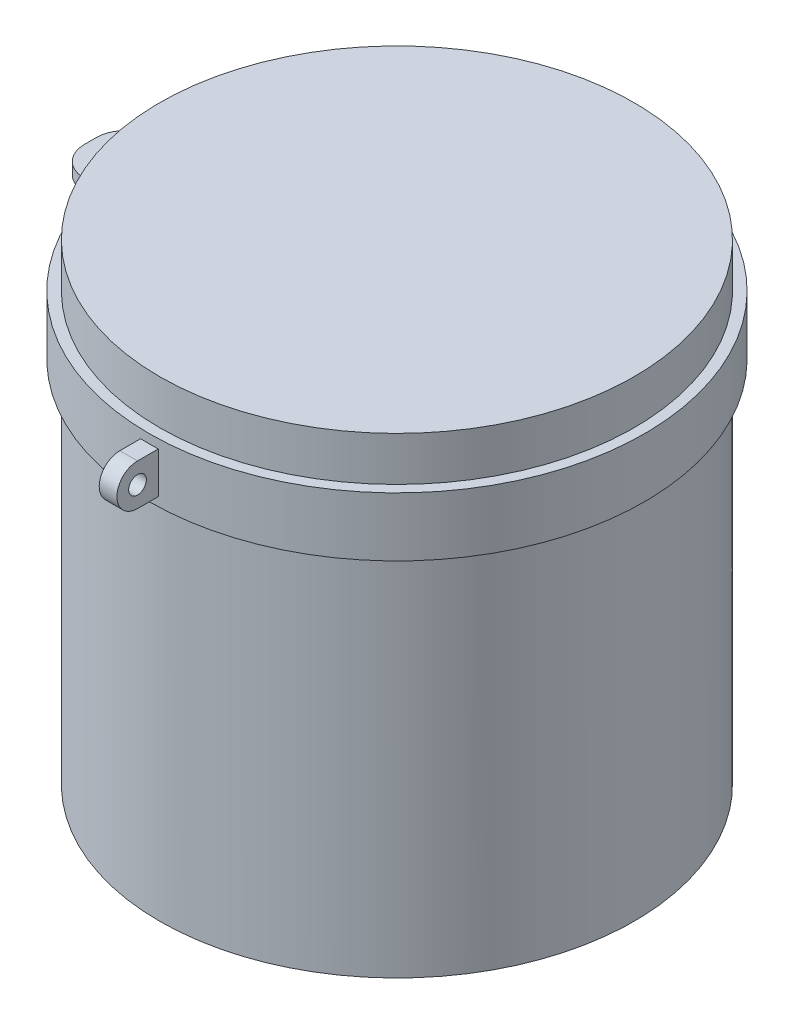
SolidWorks part; units mm, degrees
material "Серое литое железо (SN)"
ref_plane "Спереди" through (0, 0, 0) normal (0, 0, 1) x (1, 0, 0)
ref_plane "Сверху" through (0, 0, 0) normal (0, 1, 0) x (1, 0, 0)
ref_plane "Справа" through (0, 0, 0) normal (1, 0, 0) x (0, 0, -1)
sketch "Эскиз2" plane through (0, 0, 0) normal (0, 0, 1) x (1, 0, 0)
  line L0 (0, 1662.873) -> (0, -74.6932) construction
  line L2 (-800, 1450) -> (-840, 1450)
  line L3 (-800, 1450) -> (-800, 1250)
  line L4 (-800, 1250) -> (-840, 1250)
  line L5 (-840, 1450) -> (-840, 1250)
  line L6 (-975.1647, 0) -> (926.4065, 0) construction
  point P11 (0, 0)
  dimension "D1" = 800
  dimension "D2" = 200
  dimension "D3" = 40
  dimension "D4" = 1250
revolve "Повернуть2" add sketch "Эскиз2" angle 360 about L0
sketch "Эскиз3" plane through (0, 0, 0) normal (1, 0, 0) x (0, 0, -1)
  line L0 (0, 1650.3491) -> (0, -68.0955) construction
  line L1 (840, 1350) -> (1308.0457, 1350) construction
  line L2 (840, 1250) -> (840, 1450) construction
  line L3 (910, 1420) -> (800, 1420) construction
  line L4 (800, 1420) -> (800, 1280) construction
  line L5 (800, 1280) -> (910, 1280) construction
  line L6 (-800, 1280) -> (-910, 1280)
  line L7 (-910, 1420) -> (-800, 1420)
  line L8 (-800, 1420) -> (-800, 1280)
  circle A0 centre (910, 1350) radius 30 construction
  arc A1 (910, 1420) -> (910, 1280) centre (910, 1350) cw construction
  circle A2 centre (-910, 1350) radius 30
  arc A3 (-910, 1420) -> (-910, 1280) centre (-910, 1350) ccw
  dimension "D1" = 60
  dimension "D4" = 70
  dimension "D2" = 70
  dimension "D3" = 800
extrude "Бобышка-Вытянуть1" add sketch "Эскиз3" along normal mid plane 60
ref_plane "Плоскость1" through (0, 1350, 0) normal (0, 1, 0) x (1, 0, 0)
sketch "Эскиз4" plane through (0, 1350, 0) normal (0, 1, 0) x (1, 0, 0)
  line L0 (-1348.0473, 0) -> (406.526, 0) construction
  line L1 (-831.3844, 120) -> (-940, 120)
  line L2 (-1040, 20) -> (-1040, -20)
  line L3 (-831.3844, -120) -> (-940, -120)
  line L4 (-940, 416.1706) -> (-940, -609.8236) construction
  line L5 (-895, -25) -> (-895, 25)
  line L6 (-935, 65) -> (-945, 65)
  line L7 (0, 953.7064) -> (0, -1032.9554) construction
  line L8 (-840, 276.8728) -> (-840, -347.5918) construction
  line L9 (-935, -65) -> (-945, -65)
  line L10 (-985, -25) -> (-985, 25)
  circle A0 centre (0, 0) radius 840 construction
  arc A2 (-1040, 20) -> (-940, 120) centre (-940, 20) cw
  circle A3 centre (0, 0) radius 840
  arc A4 (-831.3844, 120) -> (-831.3844, -120) centre (0, 0) ccw
  arc A5 (-1040, -20) -> (-940, -120) centre (-940, -20) ccw
  arc A6 (-895, 25) -> (-935, 65) centre (-935, 25) ccw
  arc A7 (-895, -25) -> (-935, -65) centre (-935, -25) cw
  arc A8 (-985, -25) -> (-945, -65) centre (-945, -25) ccw
  arc A9 (-985, 25) -> (-945, 65) centre (-945, 25) cw
  point P15 (-1040, 0)
  point P28 (-895, 0)
  point P32 (-940, -65)
  point P37 (-940, 65)
  dimension "D2" = 100
  dimension "D6" = 40
  dimension "D3" = 45
  dimension "D4" = 65
  dimension "D5" = 100
  dimension "D7" = 100
  dimension "D8" = 120
  dimension "D1" = 0
extrude "Бобышка-Вытянуть2" add sketch "Эскиз4" along normal mid plane 40
sketch "Эскиз5" plane through (0, 0, 0) normal (0, 1, 0) x (1, 0, 0)
  line L0 (0, 899.9221) -> (0, -1122.5764) construction
  circle A0 centre (0, 0) radius 805
  dimension "D1" = 1610
ref_plane "Плоскость2" through (0, 1600, 0) normal (0, 1, 0) x (1, 0, 0)
sketch "Эскиз6" plane through (0, 1600, 0) normal (0, 1, 0) x (1, 0, 0)
  line L0 (-1264.0656, 0) -> (919.729, 0) construction
  circle A0 centre (0, 0) radius 805
  dimension "D1" = 1610
loft "По сечениям2" add profiles "Эскиз6", "Эскиз5"
